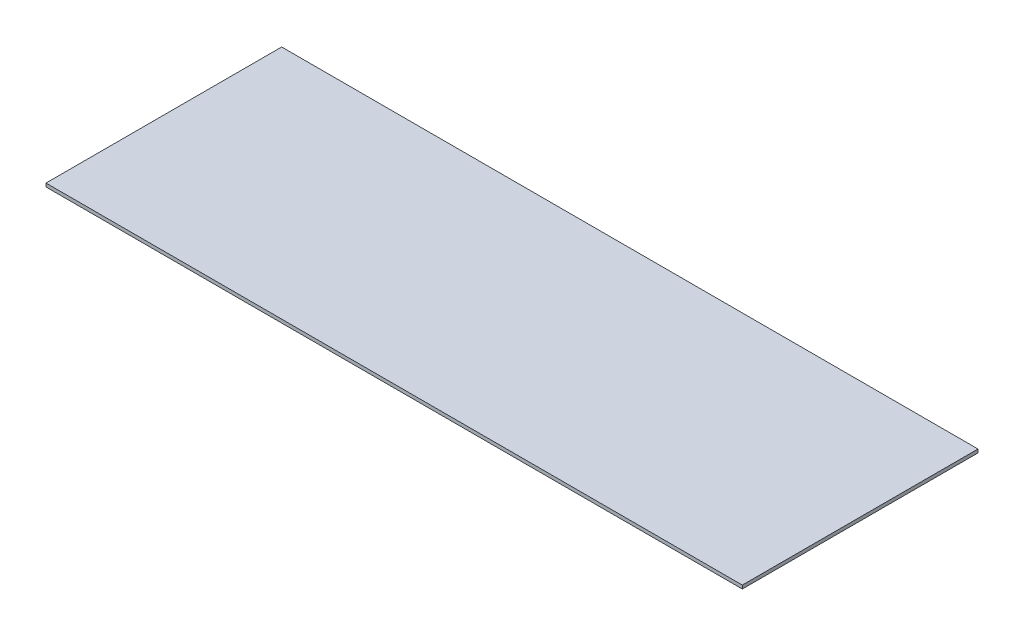
SolidWorks part; units mm, degrees
ref_plane "Front Plane" through (0, 0, 0) normal (0, 0, 1) x (1, 0, 0)
ref_plane "Top Plane" through (0, 0, 0) normal (0, 1, 0) x (1, 0, 0)
ref_plane "Right Plane" through (0, 0, 0) normal (1, 0, 0) x (0, 0, -1)
sketch "Sketch1" plane through (0, 0, 0) normal (0, 1, 0) x (1, 0, 0)
  line L1 (-97.1267, 1.0415) -> (227.8733, 1.0415)
  line L2 (-97.1267, 1.0415) -> (-97.1267, -108.9585)
  line L3 (-97.1267, -108.9585) -> (227.8733, -108.9585)
  line L4 (227.8733, 1.0415) -> (227.8733, -108.9585)
extrude "Extrude1" add sketch "Sketch1" along normal blind 1.6
